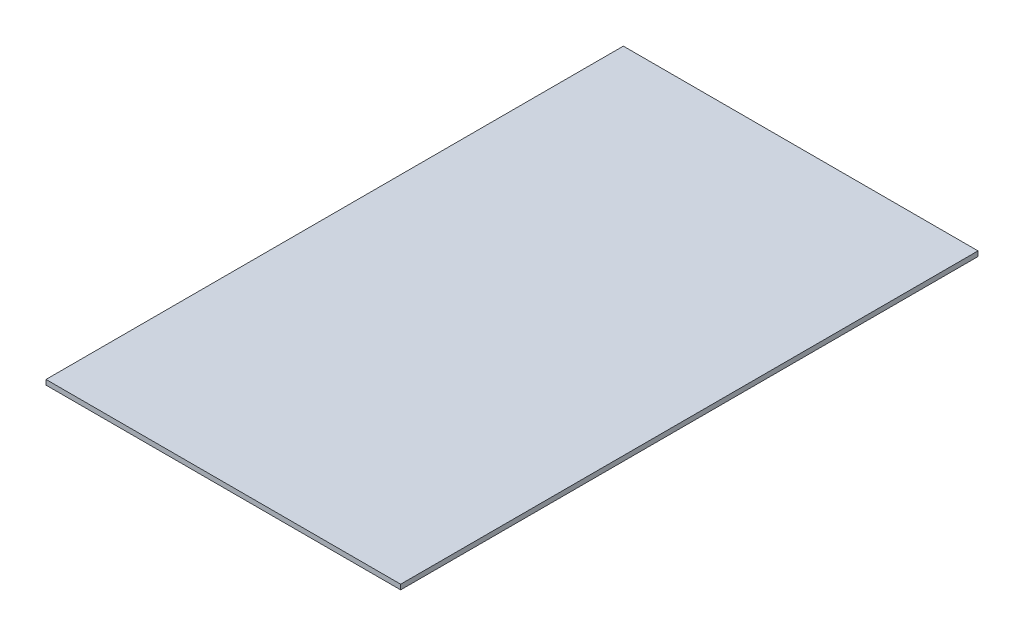
SolidWorks part; units mm, degrees
ref_plane "Front Plane" through (0, 0, 0) normal (0, 0, 1) x (1, 0, 0)
ref_plane "Top Plane" through (0, 0, 0) normal (0, 1, 0) x (1, 0, 0)
ref_plane "Right Plane" through (0, 0, 0) normal (1, 0, 0) x (0, 0, -1)
sketch "Sketch1" plane through (0, -10, 0) normal (0, -1, 0) x (1, 0, 0)
  line L1 (-107.5, 227.5) -> (107.5, 227.5)
  line L2 (-107.5, 227.5) -> (-107.5, -122.5)
  line L3 (-107.5, -122.5) -> (107.5, -122.5)
  line L4 (107.5, 227.5) -> (107.5, -122.5)
  point P6 (-106.0014, 227.5)
extrude "Boss-Extrude1" add sketch "Sketch1" along normal blind 3
